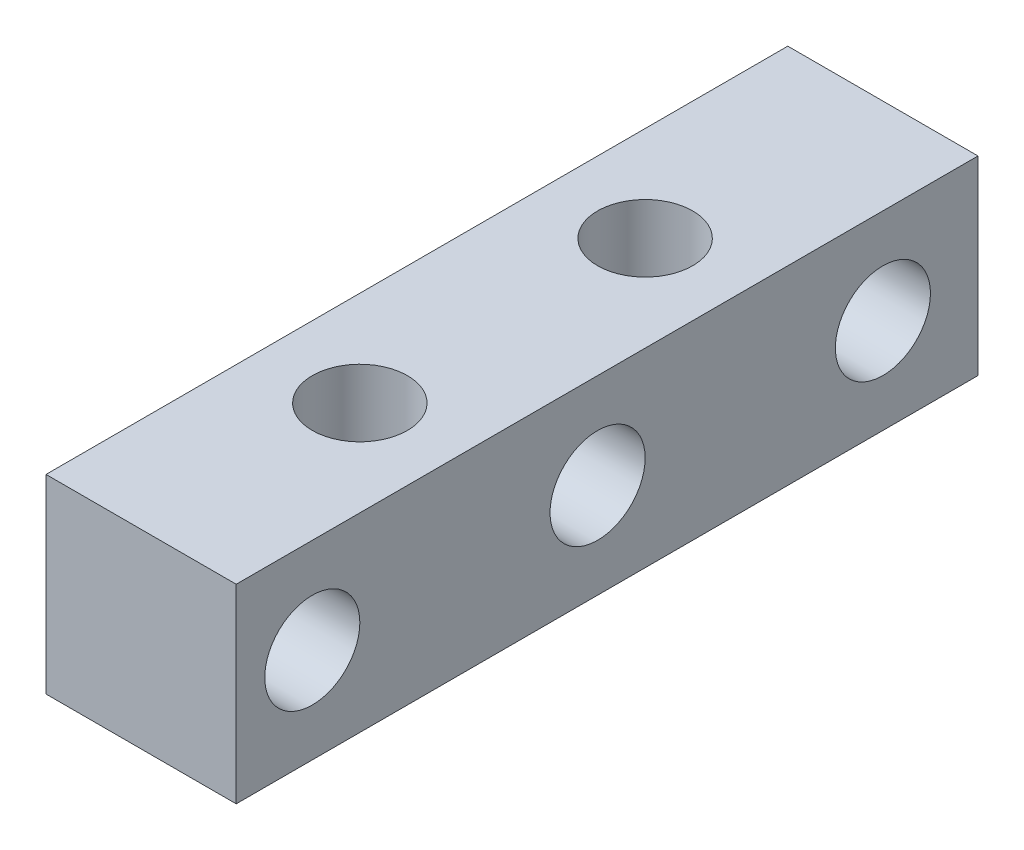
SolidWorks part; units mm, degrees
material "6061-T6 (SS)"
ref_plane "Front Plane" through (0, 0, 0) normal (0, 0, 1) x (1, 0, 0)
ref_plane "Top Plane" through (0, 0, 0) normal (0, 1, 0) x (1, 0, 0)
ref_plane "Right Plane" through (0, 0, 0) normal (1, 0, 0) x (0, 0, -1)
sketch "Sketch1" plane through (0, 0, 0) normal (0, 0, 1) x (1, 0, 0)
  line L1 (-6.35, -6.35) -> (6.35, -6.35)
  line L2 (-6.35, -6.35) -> (-6.35, 6.35)
  line L3 (-6.35, 6.35) -> (6.35, 6.35)
  line L4 (6.35, -6.35) -> (6.35, 6.35)
extrude "Boss-Extrude1" add sketch "Sketch1" along normal mid plane 69.85
hole_wizard "1/4-20 Tapped Hole1" positions "Sketch3" profile "Sketch2" tap size "1/4-20" standard "ANSI Inch" end condition through all
sketch "Sketch3" plane through (0, 6.35, 0) normal (0, 1, 0) x (1, 0, 0)
  point P0 (0, 0)
  point P3 (0, 19.05)
  point P5 (0, -19.05)
sketch "Sketch2" plane through (0, 6.35, 0) normal (1, 0, 0) x (0, 0, 1)
  line L0 (0, 0) -> (0, 12.7)
  line L1 (0, 12.7) -> (3.175, 12.7)
  line L2 (3.175, 12.7) -> (3.175, 0)
  line L5 (3.175, 0) -> (0, 0)
  line L11 (0, -6.35) -> (0, 107.95) construction
  dimension "Thread Major Dia." = 6.35
  dimension "Thru Tap Drill Depth" = 12.7
hole_wizard "1/4-20 Tapped Hole2" positions "Sketch5" profile "Sketch4" tap size "1/4-20" standard "ANSI Inch" end condition through all
sketch "Sketch5" plane through (6.35, 0, 0) normal (1, 0, 0) x (0, 0, -1)
  point P0 (9.525, 0)
  point P2 (28.575, 0)
  point P4 (-9.525, 0)
  point P6 (-28.575, 0)
  dimension "D1" = 19.05
  dimension "D2" = 19.05
  dimension "D3" = 19.05
sketch "Sketch4" plane through (6.35, 0, -9.525) normal (0, 1, 0) x (0, 0, -1)
  line L0 (0, 0) -> (0, 12.7)
  line L1 (0, 12.7) -> (3.175, 12.7)
  line L2 (3.175, 12.7) -> (3.175, 0)
  line L5 (3.175, 0) -> (0, 0)
  line L11 (0, -6.35) -> (0, 107.95) construction
  dimension "Thread Major Dia." = 6.35
  dimension "Thru Tap Drill Depth" = 12.7
sketch "Sketch6" plane through (0, 6.35, 0) normal (0, 1, 0) x (1, 0, 0)
  line L0 (6.35, -34.925) -> (6.35, 34.925) construction
  line L1 (-6.35, -34.925) -> (6.35, -34.925)
  line L2 (-6.35, -34.925) -> (-6.35, -14.605)
  line L3 (-6.35, -14.605) -> (6.35, -14.605)
  line L4 (6.35, -34.925) -> (6.35, -14.605)
  circle A1 centre (0, 0) radius 3.175 construction
  dimension "D1" = 14.605
extrude "Cut-Extrude1" cut sketch "Sketch6" against normal through all
